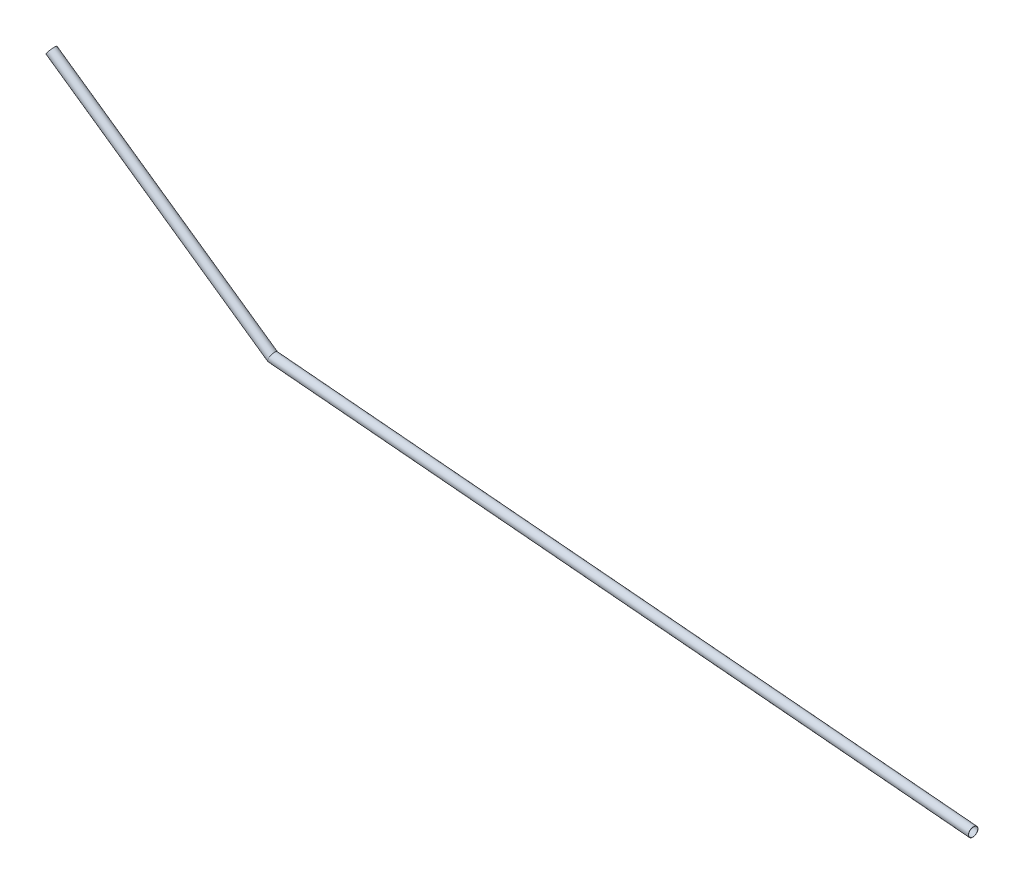
SolidWorks part; units mm, degrees
ref_plane "Front Plane" through (0, 0, 0) normal (0, 0, 1) x (1, 0, 0)
ref_plane "Top Plane" through (0, 0, 0) normal (0, 1, 0) x (1, 0, 0)
ref_plane "Right Plane" through (0, 0, 0) normal (1, 0, 0) x (0, 0, -1)
sketch "Sketch1" plane through (0, 0, 0) normal (1, 0, 0) x (0, 0, -1)
  line L0 (-8.4165, 0) -> (8.3779, 0) construction
sketch "Sketch2" plane through (0, 0, 0) normal (0, 0, 1) x (1, 0, 0)
  line L0 (-23.5253, 0) -> (23.5253, 0) construction
  line L1 (0, 0) -> (380, 33.2457)
  line L2 (380, 33.2457) -> (500, 117.2706)
  line L3 (380, 33.2457) -> (73.2093, 6.405) construction
  dimension "D1" = 5
  dimension "D2" = 30
  dimension "D3" = 500
  dimension "D4" = 380
ref_plane "Plane1" through (0, 0, 0) normal (0.9962, 0.0872, 0) x (0, 0, -1)
sketch "Sketch3" plane through (0, 0, 0) normal (0.9962, 0.0872, 0) x (0, 0, -1)
  circle A0 centre (0, 0) radius 2.5
  dimension "D1" = 5
sweep "Sweep-Thin1" add profiles "Sketch3" path "Sketch2" parameters "D1"=0.1
mirror "Mirror1" about plane through (0, 0, 0) normal (1, 0, 0) of bodies 102
delete or keep bodies "Body-Delete/Keep 1" type delete bodies bodies 102
